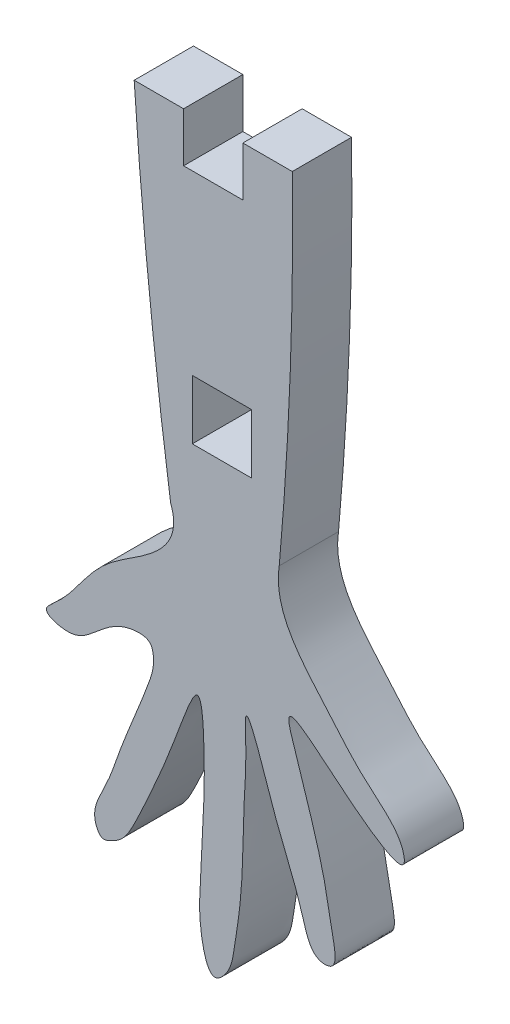
SolidWorks part; units mm, degrees
ref_plane "Front Plane" through (0, 0, 0) normal (0, 0, 1) x (1, 0, 0)
ref_plane "Top Plane" through (0, 0, 0) normal (0, 1, 0) x (1, 0, 0)
ref_plane "Right Plane" through (0, 0, 0) normal (1, 0, 0) x (0, 0, -1)
sketch "Sketch1" plane through (0, 0, 0) normal (0, 0, 1) x (1, 0, 0)
  line L0 (5.5, 0) -> (8, 0)
  line L1 (0, 0) -> (2.5, 0)
  line L3 (1.8443, -17.6108) -> (7.3409, -17.6108)
  line L4 (2.9409, -11.4653) -> (5.9409, -11.4653)
  line L5 (2.9409, -11.4653) -> (2.9409, -14.4653)
  line L6 (2.5, 0) -> (2.5, -2.5)
  line L7 (2.5, -2.5) -> (5.5, -2.5)
  line L8 (5.5, 0) -> (5.5, -2.5)
  line L9 (2.9409, -14.4653) -> (5.9409, -14.4653)
  line L10 (5.9409, -11.4653) -> (5.9409, -14.4653)
  arc A0 (8, 0) -> (7.3409, -17.6108) centre (-162.2233, -2.4468) cw
  arc A1 (0, 0) -> (1.8443, -17.6108) centre (231.4697, 15.3385) ccw
  spline S0 degree 3 poles (1.8443, -17.6108) (2.3675, -18.9451) (0.8914, -20.4729) (-1.0746, -21.5395) (-2.6076, -23.1048) (-3.2612, -24.3086) (-4.7976, -25.5577) (-3.1232, -26.0612) (-1.8554, -25.1238) (-0.7212, -23.9962) (0.783, -24.0984) (1.1107, -25.0161) (0.4194, -26.9921) (-0.5955, -29.2481) (-1.3767, -31.6837) (-2.2909, -33.1146) (-1.6394, -34.1317) (-1.1219, -33.899) (-0.4948, -33.5415) (0.0676, -32.4898) (0.8532, -30.7987) (1.7554, -28.7077) (2.3606, -27.0166) (3.405, -24.3585) (3.5813, -28.1217) (3.5144, -30.2535) (3.3596, -33.3207) (3.2411, -35.306) (3.8208, -37.7775) (4.8913, -36.6108) (5.103, -35.2427) (5.4075, -33.3551) (5.5061, -31.1824) (5.5387, -28.7208) (5.7074, -27.0005) (5.5306, -23.8751) (6.775, -27.6914) (7.5389, -29.79) (8.3987, -31.6942) (8.9403, -33.9678) (10.373, -33.8977) (9.9339, -32.087) (9.7316, -30.627) (9.2834, -28.8808) (8.737, -27.1507) (8.2986, -25.7516) (7.2859, -22.8417) (10.4389, -25.9585) (13.883, -28.2543) (13.5478, -26.6706) (12.8693, -25.7754) (11.3178, -24.5827) (9.16, -21.921) (7.0218, -19.7274) (7.3409, -17.6108) knots 0 0 0 0 0.034557 0.057171 0.068151 0.098637 0.104139 0.115965 0.128947 0.153767 0.162728 0.164167 0.182206 0.220911 0.240004 0.260619 0.265391 0.269659 0.275164 0.287715 0.303287 0.332625 0.351967 0.366761 0.389691 0.414735 0.449814 0.470499 0.487839 0.495726 0.507069 0.531104 0.551931 0.573033 0.602578 0.612823 0.644235 0.658343 0.691155 0.709442 0.713371 0.728485 0.746571 0.765207 0.780649 0.80028 0.814023 0.851718 0.88088 0.883953 0.89641 0.914328 0.942058 1 1 1 1
  dimension "D1" = 2.5
  dimension "D2" = 3
  dimension "D3" = 3
  dimension "D4" = 3
  dimension "D5" = 1.4
extrude "Boss-Extrude1" add sketch "Sketch1" along normal blind 3 contours L1 A1 L3 A0 L0 L8 L7 L6 L4 L10 L9 L5 | L3 S0
